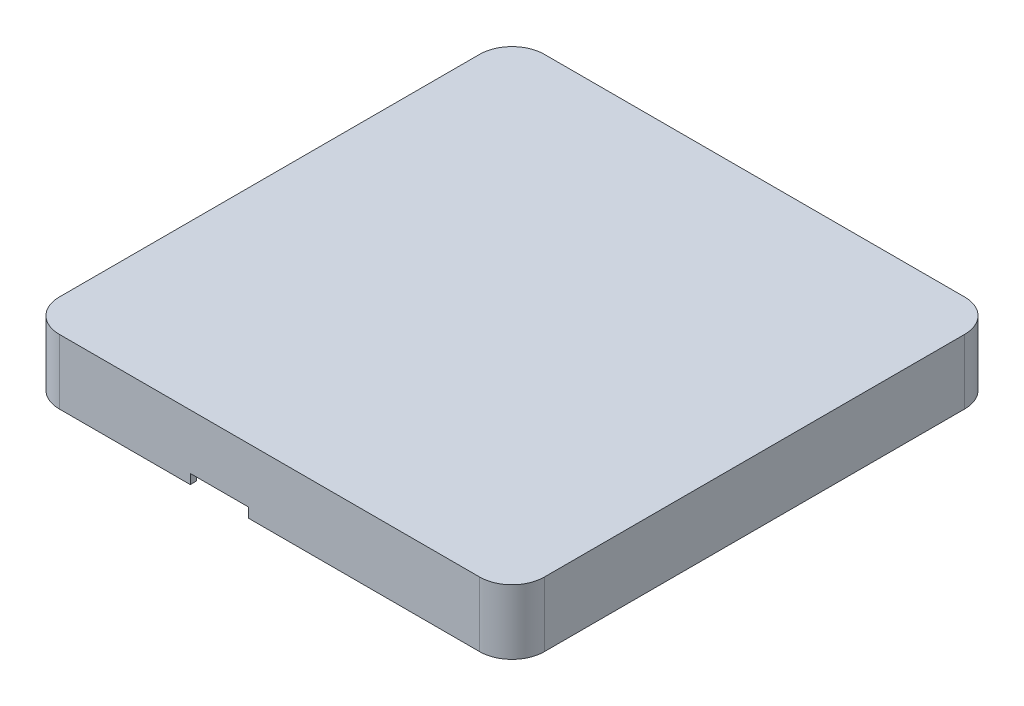
SolidWorks part; units mm, degrees
material "ABS"
ref_plane "Płaszczyzna przednia" through (0, 0, 0) normal (0, 0, 1) x (1, 0, 0)
ref_plane "Płaszczyzna górna" through (0, 0, 0) normal (0, 1, 0) x (1, 0, 0)
ref_plane "Płaszczyzna prawa" through (0, 0, 0) normal (1, 0, 0) x (0, 0, -1)
sketch "Szkic1" plane through (0, 0, 0) normal (0, 1, 0) x (1, 0, 0)
  line L0 (0, 0) -> (0, 75)
  line L1 (0, 75) -> (75, 75)
  line L2 (75, 75) -> (75, 0)
  line L3 (75, 0) -> (0, 0)
  dimension "D1" = 75
  dimension "D2" = 75
extrude "Dodanie-wyciągnięcie1" add sketch "Szkic1" along normal blind 10
fillet "Zaokrąglenie1" radius 5 4 edges at (0, 5, 0) (0, 5, -75) (75, 5, -75) (75, 5, 0)
sketch "Szkic4" plane through (0, 10, 0) normal (0, 1, 0) x (1, 0, 0)
  line L8 (2, 70) -> (2, 5)
  line L9 (5, 2) -> (70, 2)
  line L10 (73, 5) -> (73, 70)
  line L11 (70, 73) -> (5, 73)
  line L12 (2, 70) -> (2, 5)
  line L13 (5, 2) -> (70, 2)
  line L14 (73, 5) -> (73, 70)
  line L15 (70, 73) -> (5, 73)
  arc A8 (2, 5) -> (5, 2) centre (5, 5) ccw
  arc A9 (70, 2) -> (73, 5) centre (70, 5) ccw
  arc A10 (73, 70) -> (70, 73) centre (70, 70) ccw
  arc A11 (5, 73) -> (2, 70) centre (5, 70) ccw
  arc A12 (2, 5) -> (5, 2) centre (5, 5) ccw
  arc A13 (70, 2) -> (73, 5) centre (70, 5) ccw
  arc A14 (73, 70) -> (70, 73) centre (70, 70) ccw
  arc A15 (5, 73) -> (2, 70) centre (5, 70) ccw
  dimension "D1" = 2
extrude "Wytnij-wyciągnięcie1" cut sketch "Szkic4" against normal blind 8
sketch "Szkic6" plane through (0, 10, 0) normal (0, 1, 0) x (1, 0, 0)
  line L0 (2, 70) -> (2, 5)
  line L1 (5, 2) -> (70, 2)
  line L2 (73, 5) -> (73, 70)
  line L3 (70, 73) -> (5, 73)
  line L8 (1, 70) -> (1, 5)
  line L9 (5, 1) -> (70, 1)
  line L10 (74, 5) -> (74, 70)
  line L11 (70, 74) -> (5, 74)
  line L12 (1, 70) -> (1, 5)
  line L13 (5, 1) -> (70, 1)
  line L14 (74, 5) -> (74, 70)
  line L15 (70, 74) -> (5, 74)
  arc A0 (2, 5) -> (5, 2) centre (5, 5) ccw
  arc A1 (70, 2) -> (73, 5) centre (70, 5) ccw
  arc A2 (73, 70) -> (70, 73) centre (70, 70) ccw
  arc A3 (5, 73) -> (2, 70) centre (5, 70) ccw
  arc A8 (1, 5) -> (5, 1) centre (5, 5) ccw
  arc A9 (70, 1) -> (74, 5) centre (70, 5) ccw
  arc A10 (74, 70) -> (70, 74) centre (70, 70) ccw
  arc A11 (5, 74) -> (1, 70) centre (5, 70) ccw
  arc A12 (1, 5) -> (5, 1) centre (5, 5) ccw
  arc A13 (70, 1) -> (74, 5) centre (70, 5) ccw
  arc A14 (74, 70) -> (70, 74) centre (70, 70) ccw
  arc A15 (5, 74) -> (1, 70) centre (5, 70) ccw
  dimension "D1" = 1
  dimension "D2" = 1
extrude "Wytnij-wyciągnięcie2" cut sketch "Szkic6" against normal blind 4
sketch "Szkic7" plane through (0, 2, 0) normal (0, 1, 0) x (1, 0, 0)
  line L0 (2, 70) -> (2, 5) construction
  line L1 (5, 2) -> (70, 2) construction
  line L2 (5, 0) -> (70, 0) construction
  line L5 (2, 70) -> (2, 5) construction
  circle A0 centre (24, 52) radius 0.9
  circle A1 centre (35.5, 52) radius 0.9005
  circle A2 centre (24, 5) radius 0.9
  circle A3 centre (35.5, 5) radius 0.9
  circle A4 centre (24, 52) radius 1.9
  circle A5 centre (35.5, 52) radius 1.9005
  circle A6 centre (35.5, 5) radius 1.9
  circle A7 centre (24, 5) radius 1.9
  point P22 (0, 0)
  dimension "D1" = 22
  dimension "D3" = 1.8
  dimension "D5" = 1.801
  dimension "D7" = 1.8
  dimension "D10" = 11.5
  dimension "D11" = 1.8
  dimension "D2" = 3
  dimension "D4" = 11.5
  dimension "D6" = 5
  dimension "D8" = 47
  dimension "D9" = 22
  dimension "D12" = 47
  dimension "D13" = 1
extrude "Dodanie-wyciągnięcie2" add sketch "Szkic7" along normal blind 8.7
sketch "Szkic9" plane through (0, 2, 0) normal (0, 1, 0) x (1, 0, 0)
  line L4 (2, 70) -> (2, 5)
  line L5 (5, 2) -> (70, 2)
  line L6 (73, 5) -> (73, 70)
  line L7 (70, 73) -> (5, 73)
  line L8 (2, 70) -> (2, 5)
  line L9 (5, 2) -> (70, 2)
  line L10 (73, 5) -> (73, 70)
  line L11 (70, 73) -> (5, 73)
  circle A0 centre (35.5, 52) radius 0.9005 construction
  circle A1 centre (35.5, 52) radius 0.9005
  circle A2 centre (35.5, 5) radius 0.9 construction
  circle A3 centre (24, 5) radius 0.9 construction
  arc A4 (5, 73) -> (2, 70) centre (5, 70) ccw
  arc A5 (2, 5) -> (5, 2) centre (5, 5) ccw
  arc A6 (70, 2) -> (73, 5) centre (70, 5) ccw
  arc A7 (73, 70) -> (70, 73) centre (70, 70) ccw
  arc A8 (5, 73) -> (2, 70) centre (5, 70) ccw
  arc A9 (2, 5) -> (5, 2) centre (5, 5) ccw
  arc A10 (70, 2) -> (73, 5) centre (70, 5) ccw
  arc A11 (73, 70) -> (70, 73) centre (70, 70) ccw
  circle A12 centre (24, 52) radius 0.9 construction
  circle A13 centre (35.5, 5) radius 0.9
  circle A14 centre (24, 5) radius 0.9
  circle A15 centre (24, 52) radius 0.9
  dimension "D1" = 0
extrude "Dodanie-wyciągnięcie3" add sketch "Szkic9" along normal blind 1 contours A15 | A1 | A14 | A13
sketch "Szkic10" plane through (0, 2, 0) normal (0, 1, 0) x (1, 0, 0)
  line L0 (73, 5) -> (73, 70) construction
  line L1 (5, 2) -> (70, 2) construction
  line L2 (5, 2) -> (70, 2) construction
  circle A0 centre (67, 17) radius 1.7
  circle A1 centre (67, 8) radius 1.7
  dimension "D1" = 3.4
  dimension "D2" = 3.4
  dimension "D4" = 6
  dimension "D3" = 9
  dimension "D5" = 6
  dimension "D6" = 15
extrude "Dodanie-wyciągnięcie4" add sketch "Szkic10" along normal blind 1
sketch "Szkic11" plane through (0, 2, 0) normal (0, 1, 0) x (1, 0, 0)
  line L4 (2, 70) -> (2, 5)
  line L5 (5, 2) -> (70, 2)
  line L6 (73, 5) -> (73, 70)
  line L7 (70, 73) -> (5, 73)
  line L8 (2, 70) -> (2, 5)
  line L9 (5, 2) -> (70, 2)
  line L10 (73, 5) -> (73, 70)
  line L11 (70, 73) -> (5, 73)
  circle A0 centre (67, 8) radius 1.7 construction
  circle A1 centre (67, 17) radius 1.7 construction
  circle A2 centre (67, 8) radius 1.7
  circle A3 centre (67, 17) radius 1.7
  arc A4 (5, 73) -> (2, 70) centre (5, 70) ccw
  arc A5 (2, 5) -> (5, 2) centre (5, 5) ccw
  arc A6 (70, 2) -> (73, 5) centre (70, 5) ccw
  arc A7 (73, 70) -> (70, 73) centre (70, 70) ccw
  arc A8 (5, 73) -> (2, 70) centre (5, 70) ccw
  arc A9 (2, 5) -> (5, 2) centre (5, 5) ccw
  arc A10 (70, 2) -> (73, 5) centre (70, 5) ccw
  arc A11 (73, 70) -> (70, 73) centre (70, 70) ccw
  circle A12 centre (67, 17) radius 2.45
  circle A13 centre (67, 8) radius 2.45
  circle M9 centre (67, 8) radius 1.7
  circle M10 centre (67, 17) radius 1.7
  dimension "D1" = 0
  dimension "D2" = 0.75
extrude "Dodanie-wyciągnięcie5" add sketch "Szkic11" along normal blind 8.5 contours A12 M10 | A13 M9
ref_plane "Płaszczyzna1" through (0, -10, 0) normal (0, 1, 0) x (1, 0, 0)
sketch "Szkic19" plane through (0, 0, -2) normal (0, 0, -1) x (-1, 0, 0)
  line L0 (-29.75, 10) -> (-29.75, 2) construction
  line L1 (-5, 2) -> (-70, 2) construction
  line L2 (-5, 2) -> (-5, 6) construction
  line L3 (-2, 2) -> (-2, 6) construction
  line L4 (-5, 10) -> (-70, 10) construction
  line L8 (-5, 10) -> (-70, 10) construction
  line L9 (-34.25, 10) -> (-25.25, 10)
  line L10 (-34.25, 10) -> (-34.25, 8.5)
  line L11 (-34.25, 8.5) -> (-25.25, 8.5)
  line L12 (-25.25, 10) -> (-25.25, 8.5)
  point P18 (0, 0)
  dimension "D1" = 27.75
  dimension "D3" = 4.5
  dimension "D4" = 9
  dimension "D5" = 1.5
  dimension "D6" = 0
extrude "Wytnij-wyciągnięcie15" cut sketch "Szkic19" against normal blind 10
sketch "Szkic22" plane through (74, 0, 0) normal (-1, 0, 0) x (0, 0, 1)
  line L0 (-39.5, 9) -> (-35.5, 9)
  line L1 (-65, 9) -> (-61, 9)
  line L2 (-65, 9) -> (-65, 10)
  line L3 (-65, 10) -> (-61, 10)
  line L4 (-61, 9) -> (-61, 10)
  line L5 (-75, 10) -> (-75, 0) construction
  line L6 (-14, 9) -> (-14, 10)
  line L7 (-14, 10) -> (-10, 10)
  line L8 (-10, 9) -> (-10, 10)
  line L9 (-14, 9) -> (-10, 9)
  line L10 (0, 0) -> (0, 10) construction
  line L11 (-5, 10) -> (-70, 10) construction
  line L12 (-39.5, 9) -> (-39.5, 10)
  line L13 (-39.5, 10) -> (-35.5, 10)
  line L14 (-35.5, 9) -> (-35.5, 10)
  point P14 (-63, 9)
  point P19 (-37.5, 9)
  dimension "D1" = 4
  dimension "D2" = 1
  dimension "D3" = 10
  dimension "D5" = 10
  dimension "D7" = 25.5
  dimension "D4" = 2
  dimension "D6" = 2
extrude "Dodanie-wyciągnięcie6" add sketch "Szkic22" along normal blind 0.3
ref_plane "Płaszczyzna2" through (1, 10, -5) normal (0, 0, 1) x (1, 0, 0)
sketch "Szkic24" plane through (1, 0, 0) normal (1, 0, 0) x (0, 0, -1)
  line L0 (70, 10) -> (5, 10) construction
  line L1 (10, 10) -> (14, 10)
  line L2 (10, 10) -> (10, 9)
  line L3 (10, 9) -> (14, 9)
  line L4 (14, 10) -> (14, 9)
  line L5 (0, 10) -> (0, 0) construction
  line L6 (61, 10) -> (65, 10)
  line L7 (61, 9) -> (65, 9)
  line L8 (61, 10) -> (61, 9)
  line L9 (65, 10) -> (65, 9)
  line L10 (75, 0) -> (75, 10) construction
  line L11 (35.5, 10) -> (35.5, 9)
  line L12 (35.5, 10) -> (39.5, 10)
  line L13 (35.5, 9) -> (39.5, 9)
  line L14 (39.5, 10) -> (39.5, 9)
  point P15 (12, 9)
  point P19 (37.5, 9)
  dimension "D1" = 4
  dimension "D2" = 1
  dimension "D3" = 10
  dimension "D5" = 10
  dimension "D7" = 25.5
  dimension "D4" = 2
  dimension "D6" = 2
extrude "Dodanie-wyciągnięcie7" add sketch "Szkic24" along normal blind 0.3
sketch "Szkic25" plane through (0, 0, -10) normal (0, 0, 1) x (1, 0, 0)
  line L0 (1, 10) -> (1.3, 9.5)
  line L1 (1.3, 10) -> (1.3, 9) construction
  line L2 (1, 10) -> (1.3, 10)
  line L3 (1.3, 10) -> (1.3, 9.5)
extrude "Wytnij-wyciągnięcie13" cut sketch "Szkic25" against normal blind 55
sketch "Szkic26" plane through (0, 0, -65) normal (0, 0, -1) x (-1, 0, 0)
  line L0 (-74, 10) -> (-73.7, 10)
  line L1 (-73.7, 10) -> (-73.7, 9.5)
  line L2 (-73.7, 10) -> (-73.7, 9) construction
  line L3 (-73.7, 9.5) -> (-74, 10)
extrude "Wytnij-wyciągnięcie14" cut sketch "Szkic26" against normal blind 55
mirror "Lustro5" about plane through (0, -10, 0) normal (0, 1, 0) of bodies 133 137
delete or keep bodies "Obiekt-Usuń/zachowaj 1" type delete bodies bodies 133
